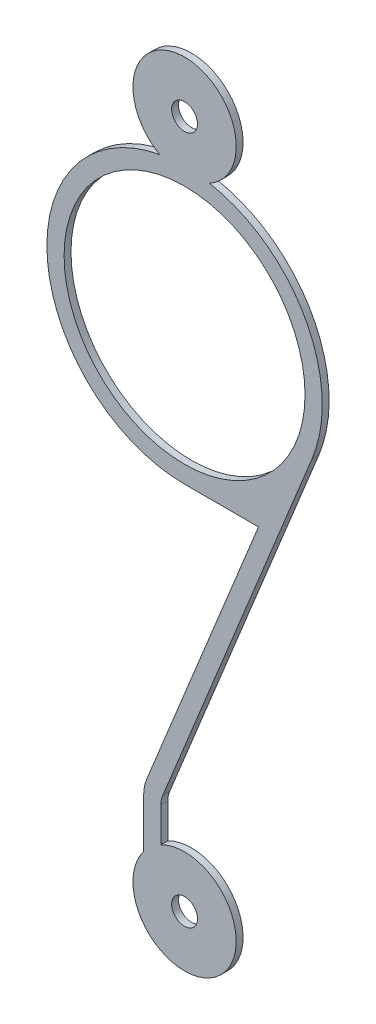
SolidWorks part; units mm, degrees
material "3.0517 (EN-AW 3003)"
ref_plane "Front Plane" through (0, 0, 0) normal (0, 0, 1) x (1, 0, 0)
ref_plane "Top Plane" through (0, 0, 0) normal (0, 1, 0) x (1, 0, 0)
ref_plane "Right Plane" through (0, 0, 0) normal (1, 0, 0) x (0, 0, -1)
sketch "Sketch1" plane through (0, 0, 0) normal (0, 0, 1) x (1, 0, 0)
  line L0 (0, -10) -> (0, 10) construction
  line L1 (4, 8.75) -> (-4, 8.75) construction
  line L2 (4, 8.75) -> (4, 4.75) construction
  line L3 (-4, 8.75) -> (-4, 4.75) construction
  line L4 (-0.6875, -10) -> (-0.6875, -7.6668) construction
  line L5 (-0.6875, -10) -> (-1.1875, -10) construction
  line L6 (-1.1875, -10) -> (-1.1875, -7.6668) construction
  line L7 (-0.375, -10) -> (-0.6875, -10) construction
  line L8 (-0.6366, -7.4073) -> (3.704, 3.24)
  line L9 (-1.0996, -7.2185) -> (2.149, 0.75)
  line L10 (-1.1875, -7.6668) -> (-1.1875, -9.0836)
  line L11 (-0.6875, -7.6668) -> (-0.6875, -8.6668)
  line L12 (-1.1875, -10) -> (-1.5, -10) construction
  line L13 (0, 0.75) -> (2.149, 0.75)
  arc A0 (-1.1875, -9.0836) -> (-0.6875, -8.6668) centre (0, -10) ccw
  circle A1 centre (0, -10) radius 0.375
  arc A2 (0.7208, 8.6845) -> (-0.7208, 8.6845) centre (0, 10) ccw
  circle A3 centre (0, 10) radius 0.375
  arc A4 (3.704, 3.24) -> (0.7208, 8.6845) centre (0, 4.75) ccw
  arc A5 (-0.6875, -7.6668) -> (-0.6366, -7.4073) centre (0, -7.6668) cw
  arc A6 (-1.1875, -7.6668) -> (-1.0996, -7.2185) centre (0, -7.6668) cw
  circle A7 centre (0, 4.75) radius 3.5
  arc A9 (-0.7208, 8.6845) -> (0, 0.75) centre (0, 4.75) ccw
  point P9 (0, 8.75)
  dimension "D2" = 3
  dimension "D3" = 0.75
  dimension "D4" = 8
  dimension "D6" = 0.5
  dimension "D1" = 20
  dimension "D5" = 1.25
  dimension "D8" = 1
extrude "Boss-Extrude1" add sketch "Sketch1" along normal mid plane 0.2
sketch "Sketch2" plane through (0, 0, 0) normal (0, 0, 1) x (1, 0, 0)
  line L5 (-1.4375, -9.5715) -> (-0.4375, -8.5652)
  line L10 (0, 0.5) -> (1.7771, 0.5)
  line L11 (1.7771, 0.5) -> (-1.3311, -7.1242)
  line L12 (-1.4375, -7.6668) -> (-1.4375, -9.002)
  line L13 (-0.4375, -8.3056) -> (-0.4375, -7.6668)
  line L14 (-0.4051, -7.5017) -> (3.9355, 3.1456)
  line L15 (0, 0.5) -> (1.7771, 0.5)
  line L16 (1.7771, 0.5) -> (-1.3311, -7.1242)
  line L17 (-1.4375, -7.6668) -> (-1.4375, -9.5715)
  line L18 (-0.4375, -8.5652) -> (-0.4375, -7.6668)
  line L19 (-0.4051, -7.5017) -> (3.9355, 3.1456)
  arc A6 (-1.1875, -9.0836) -> (-0.6875, -8.6668) centre (0, -10) ccw construction
  arc A7 (-1.1875, -9.0836) -> (-0.6875, -8.6668) centre (0, -10) ccw construction
  circle A10 centre (0, 4.75) radius 3.25
  circle A11 centre (0, 4.75) radius 3.25
  arc A12 (-1.2771, 8.8036) -> (0, 0.5) centre (0, 4.75) ccw
  arc A13 (-1.3311, -7.1242) -> (-1.4375, -7.6668) centre (0, -7.6668) ccw
  arc A14 (-1.4375, -9.002) -> (-0.4375, -8.3056) centre (0, -10) ccw
  arc A15 (-0.4051, -7.5017) -> (-0.4375, -7.6668) centre (0, -7.6668) ccw
  arc A16 (3.9355, 3.1456) -> (1.2771, 8.8036) centre (0, 4.75) ccw
  arc A17 (1.2771, 8.8036) -> (-1.2771, 8.8036) centre (0, 10) ccw
  arc A18 (0, 9) -> (0, 0.5) centre (0, 4.75) ccw
  arc A19 (-1.3311, -7.1242) -> (-1.4375, -7.6668) centre (0, -7.6668) ccw
  arc A21 (-0.4051, -7.5017) -> (-0.4375, -7.6668) centre (0, -7.6668) ccw
  arc A22 (3.9355, 3.1456) -> (0, 9) centre (0, 4.75) ccw
  dimension "D2" = 0.25
  dimension "D1" = 0.25
extrude "Boss-Extrude2" [suppressed] add sketch "Sketch2" along normal mid plane 0.6
